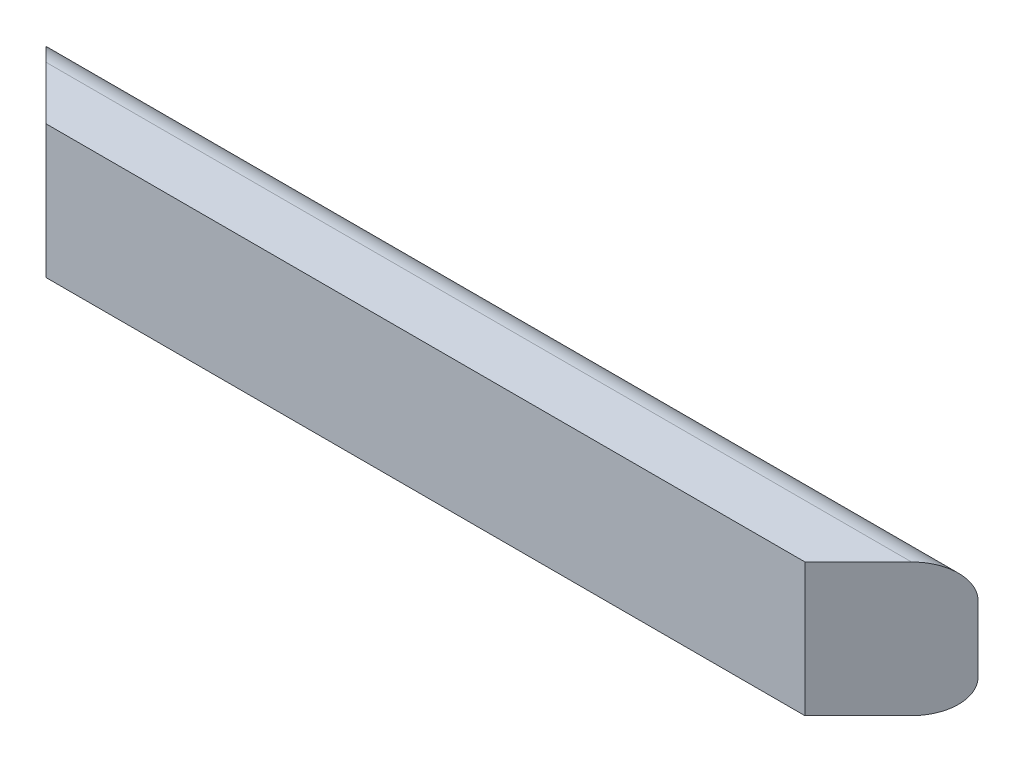
SolidWorks part; units mm, degrees
ref_plane "Front" through (0, 0, 0) normal (0, 0, 1) x (1, 0, 0)
ref_plane "Top" through (0, 0, 0) normal (0, 1, 0) x (1, 0, 0)
ref_plane "Right" through (0, 0, 0) normal (1, 0, 0) x (0, 0, -1)
sketch "Sketch1" plane through (0, 0, 0) normal (1, 0, 0) x (0, 0, -1)
  line L0 (0, 0) -> (0, 127) construction
  line L1 (0, 0) -> (31.75, 0)
  line L2 (31.75, 127) -> (0, 127)
  line L3 (63.5, 95.25) -> (63.5, 31.75)
  line L4 (0, 0) -> (-19.05, 0)
  line L5 (-19.05, 0) -> (-19.05, 127)
  line L6 (-19.05, 127) -> (0, 127)
  arc A0 (31.75, 0) -> (63.5, 31.75) centre (31.75, 31.75) ccw
  arc A1 (63.5, 95.25) -> (31.75, 127) centre (31.75, 95.25) ccw
  dimension "D2" = 63.5
  dimension "D1" = 19.05
extrude "Boss-Extrude1" add sketch "Sketch1" along normal blind 888.6444
ref_plane "Mid_Plane" through (444.3222, 0, 0) normal (1, 0, 0) x (0, 0, -1)
ref_plane "Plane1" through (412.5722, 0, 412.5722) normal (0.7071, 0, 0.7071) x (0, 1, 0)
sketch "Sketch2" plane through (412.5722, 0, 412.5722) normal (0.7071, 0, 0.7071) x (0, 1, 0)
  line L0 (31.75, -673.2678) -> (95.25, -673.2678) construction
  line L1 (205.1964, -283.039) -> (-139.2061, -283.039)
  line L2 (205.1964, -283.039) -> (205.1964, -1063.4965)
  line L3 (205.1964, -1063.4965) -> (-139.2061, -1063.4965)
  line L4 (-139.2061, -283.039) -> (-139.2061, -1063.4965)
  line L5 (205.1964, -283.039) -> (-139.2061, -1063.4965) construction
  line L6 (205.1964, -1063.4965) -> (-139.2061, -283.039) construction
  point P4 (32.9952, -673.2678)
extrude "Cut-Extrude1" cut sketch "Sketch2" along normal through all
mirror "Mirror1" about plane through (444.3222, 0, 0) normal (1, 0, 0) of "Cut-Extrude1"
